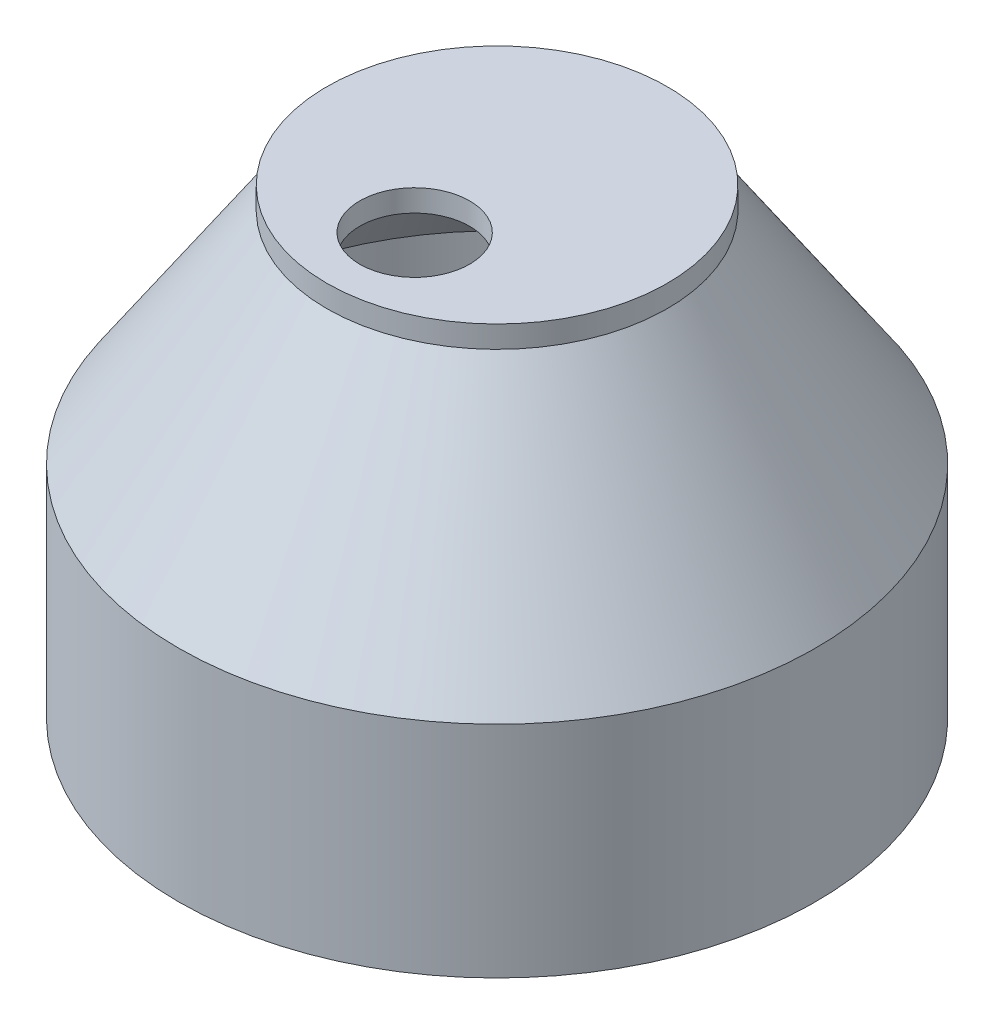
SolidWorks part; units mm, degrees
ref_plane "Ön Düzlem" through (0, 0, 0) normal (0, 0, 1) x (1, 0, 0)
ref_plane "Üst Düzlem" through (0, 0, 0) normal (0, 1, 0) x (1, 0, 0)
ref_plane "Sağ Düzlem" through (0, 0, 0) normal (1, 0, 0) x (0, 0, -1)
sketch "Çizim5" plane through (0, 0, 0) normal (1, 0, 0) x (0, 0, -1)
  line L0 (12.5, 20) -> (15.5, 20)
  line L1 (15.5, 20) -> (29, 0)
  line L2 (29, 0) -> (29, -20)
  line L3 (29, -20) -> (26, -20)
  line L4 (26, -20) -> (26, 0)
  line L5 (26, 0) -> (12.5, 20)
  line L6 (0, 40.2843) -> (0, -47.2424) construction
  dimension "D1" = 20
  dimension "D2" = 20
  dimension "D3" = 20
  dimension "D4" = 3
  dimension "D5" = 26
  dimension "D6" = 12.5
revolve "Döndür1" add sketch "Çizim5" angle 360 about L6
sketch "Çizim6" plane through (0, 20, 0) normal (0, 1, 0) x (1, 0, 0)
  circle A0 centre (0, 0) radius 15.5
  circle A1 centre (0, -7.5) radius 5
  circle A2 centre (0, 0) radius 12.5 construction
  dimension "D1" = 10
extrude "Yükseklik-Ekstrüzyon2" add sketch "Çizim6" along normal blind 2
